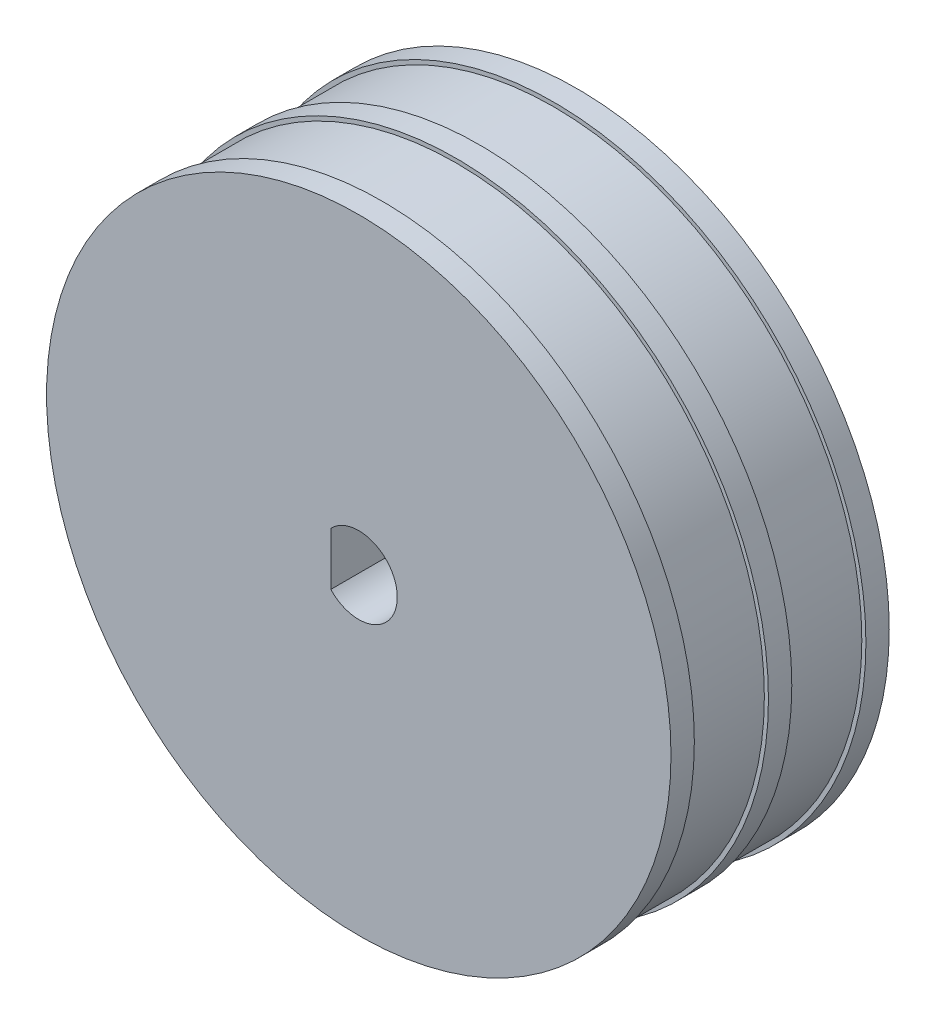
SolidWorks part; units mm, degrees
material "ABS"
ref_plane "Front Plane" through (0, 0, 0) normal (0, 0, 1) x (1, 0, 0)
ref_plane "Top Plane" through (0, 0, 0) normal (0, 1, 0) x (1, 0, 0)
ref_plane "Right Plane" through (0, 0, 0) normal (1, 0, 0) x (0, 0, -1)
sketch "Sketch2" plane through (0, 0, 0) normal (0, 0, 1) x (1, 0, 0)
  circle A0 centre (0, 0) radius 13.375
  dimension "D1" = 26.75
extrude "Boss-Extrude1" add sketch "Sketch2" along normal blind 1
sketch "Sketch3" plane through (0, 0, 1) normal (0, 0, 1) x (1, 0, 0)
  circle A0 centre (0, 0) radius 13.2
  dimension "D1" = 26.4
extrude "Boss-Extrude2" add sketch "Sketch3" along normal blind 3.175
sketch "Sketch4" plane through (0, 0, 4.175) normal (0, 0, 1) x (1, 0, 0)
  circle A0 centre (0, 0) radius 13.375 construction
  circle A1 centre (0, 0) radius 13.375
extrude "Boss-Extrude3" add sketch "Sketch4" along normal blind 1
sketch "Sketch5" plane through (0, 0, 5.175) normal (0, 0, 1) x (1, 0, 0)
  circle A0 centre (0, 0) radius 13.2 construction
  circle A1 centre (0, 0) radius 13.2
extrude "Boss-Extrude4" add sketch "Sketch5" along normal blind 3.175
sketch "Sketch6" plane through (0, 0, 8.35) normal (0, 0, 1) x (1, 0, 0)
  circle A0 centre (0, 0) radius 13.375 construction
  circle A1 centre (0, 0) radius 13.375
extrude "Boss-Extrude5" add sketch "Sketch6" along normal blind 1
sketch "Sketch7" plane through (0, 0, 9.35) normal (0, 0, 1) x (1, 0, 0)
  line L0 (-1, 1.118) -> (-1, -1.118)
  line L1 (0, 0) -> (0, 13.375) construction
  line L2 (0, 0) -> (13.375, 0) construction
  line L3 (0.5, 0.5) -> (0.5, 10.5)
  line L4 (0.5, 0.5) -> (10.5, 0.5)
  line L5 (10.5, 0.5) -> (0.5, 10.5)
  line L6 (0.5, 11.2389) -> (11.2389, 0.5)
  line L7 (11.2389, -0.5) -> (0.5, -11.2389)
  line L8 (0.5, -10.5) -> (10.5, -0.5)
  line L9 (0.5, -0.5) -> (10.5, -0.5)
  line L10 (0.5, -0.5) -> (0.5, -10.5)
  line L11 (-0.5, -11.2389) -> (-11.2389, -0.5)
  line L12 (-10.5, -0.5) -> (-0.5, -10.5)
  line L13 (-0.5, -0.5) -> (-0.5, -10.5)
  line L14 (-0.5, -0.5) -> (-10.5, -0.5)
  line L15 (-11.2389, 0.5) -> (-0.5, 11.2389)
  line L16 (-0.5, 10.5) -> (-10.5, 0.5)
  line L17 (-0.5, 0.5) -> (-10.5, 0.5)
  line L18 (-0.5, 0.5) -> (-0.5, 10.5)
  line L23 (-6.3998, 5.3391) -> (-5.3391, 6.3998)
  line L27 (1.156, 2.2167) -> (2.2167, 1.156)
  line L28 (1.156, 2.2167) -> (8.0801, 9.1407)
  line L29 (2.2167, 1.156) -> (9.1407, 8.0801)
  line L30 (8.0801, 9.1407) -> (9.1407, 8.0801)
  line L31 (2.2167, -1.156) -> (1.156, -2.2167)
  line L32 (2.2167, -1.156) -> (9.1407, -8.0801)
  line L33 (9.1407, -8.0801) -> (8.0801, -9.1407)
  line L34 (1.156, -2.2167) -> (8.0801, -9.1407)
  line L35 (-1.156, -2.2167) -> (-2.2167, -1.156)
  line L36 (-1.156, -2.2167) -> (-8.0801, -9.1407)
  line L37 (-8.0801, -9.1407) -> (-9.1407, -8.0801)
  line L38 (-2.2167, -1.156) -> (-9.1407, -8.0801)
  line L39 (-2.2167, 1.156) -> (-1.156, 2.2167)
  line L40 (-2.2167, 1.156) -> (-9.1407, 8.0801)
  line L41 (-9.1407, 8.0801) -> (-8.0801, 9.1407)
  line L42 (-1.156, 2.2167) -> (-8.0801, 9.1407)
  arc A0 (-1, -1.118) -> (-1, 1.118) centre (0, 0) ccw
  circle A1 centre (0, 0) radius 2.5
  circle A2 centre (0, 0) radius 13.375 construction
  circle A3 centre (0, 0) radius 12.2
  circle A4 centre (0, 0) radius 12.2
  arc A5 (11.2389, 0.5) -> (0.5, 11.2389) centre (0, 0) ccw
  arc A6 (0.5, -11.2389) -> (11.2389, -0.5) centre (0, 0) ccw
  arc A7 (-11.2389, -0.5) -> (-0.5, -11.2389) centre (0, 0) ccw
  arc A8 (-0.5, 11.2389) -> (-11.2389, 0.5) centre (0, 0) ccw
  point P13 (0.5, 0.5)
  point P14 (-5.8694, 5.8694)
  point P37 (0, 0)
  point P38 (-5.8694, 5.8694)
  point P56 (0, 0)
  point P59 (0, 0)
  dimension "D1" = 3
  dimension "D4" = 5
  dimension "D8" = 22.5
  dimension "D2" = 1
  dimension "D5" = 0.5
  dimension "D6" = 0.5
  dimension "D7" = 10
  dimension "D10" = 1.5
  dimension "D3" = 1
  dimension "D9" = 4
  dimension "D11" = 4
extrude "Cut-Extrude1" [suppressed] cut sketch "Sketch7" against normal blind 10 contours L40 A8 L15 | L15 A8 L42 | A1 L18 L16 L42 | A1 L40 L16 L17 | A1 L14 L12 L38 | L11 A7 L38 | L36 A7 L11 | A1 L36 L12 L13 | A1 L10 L8 L34 | A1 L32 L8 L9 | A1 L4 L5 L29 | A1 L28 L5 L3 | L28 A5 L6 | L6 A5 L29 | L32 A6 L7 | L7 A6 L34 | L3 A0 L18 L17 L0 L14 L13 L10 L9 L4 | L4 A0 L3 | L18 A0 L0 L17 | L0 A0 L13 L14 | L10 A0 L9
sketch "Sketch8" plane through (0, 0, 0) normal (0, 0, -1) x (-1, 0, 0)
  line L0 (1, 1.05) -> (1, -1.05) construction
  line L1 (1.2, 1.1325) -> (1.2, -1.1325)
  arc A1 (1, 1.05) -> (1, -1.05) centre (0, 0) ccw construction
  arc A2 (1.2, 1.1325) -> (1.2, -1.1325) centre (0, 0) ccw
  dimension "D1" = 0.2
  dimension "D2" = 2.9
  dimension "D3" = 1
extrude "Cut-Extrude2" cut sketch "Sketch8" against normal through all
